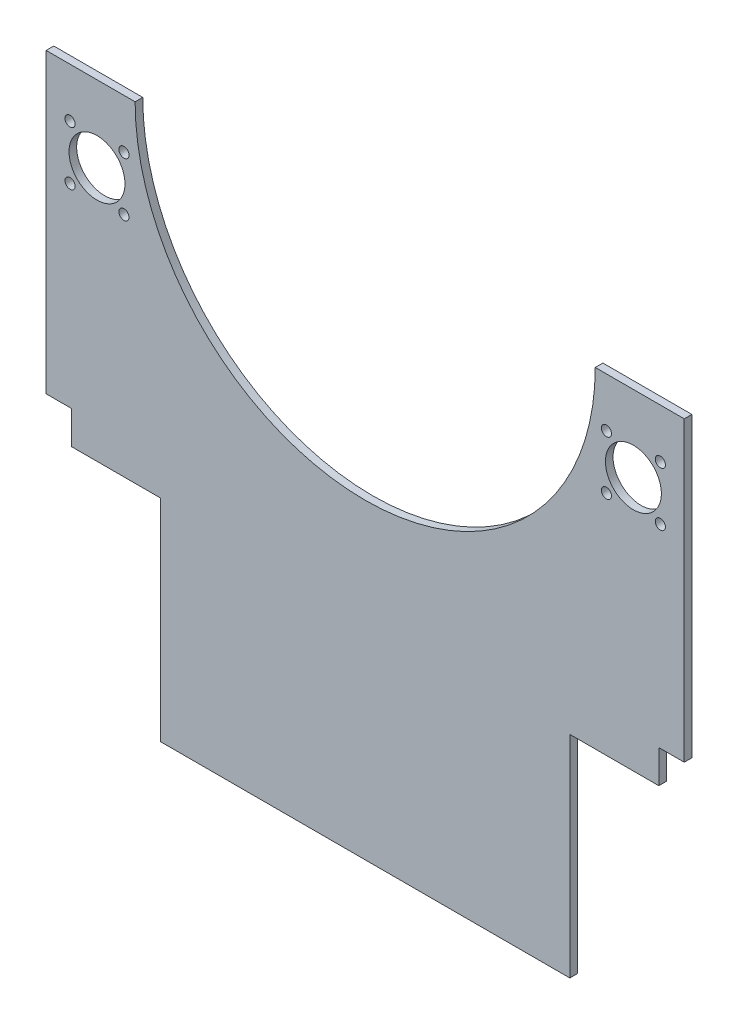
SolidWorks part; units mm, degrees
ref_plane "Plan de face" through (0, 0, 0) normal (0, 0, 1) x (1, 0, 0)
ref_plane "Plan de dessus" through (0, 0, 0) normal (0, 1, 0) x (1, 0, 0)
ref_plane "Plan de droite" through (0, 0, 0) normal (1, 0, 0) x (0, 0, -1)
sketch "Esquisse1" plane through (0, 0, 0) normal (0, 0, 1) x (1, 0, 0)
  line L0 (125.5, 0) -> (125.5, -117)
  line L1 (-90.5, 0) -> (-125.5, 0)
  line L2 (90.5, 0) -> (125.5, 0)
  line L3 (0, 0) -> (0, -135.6456) construction
  line L4 (125.5, -117) -> (115.5, -117)
  line L5 (-80.5, -213) -> (80.5, -213)
  line L6 (-115.5, -130) -> (-80.5, -130)
  line L7 (-80.5, -130) -> (-80.5, -213)
  line L8 (110.5, -30) -> (133.6301, -30) construction
  line L9 (-125.5, -117) -> (-115.5, -117)
  line L10 (80.5, -130) -> (80.5, -213)
  line L11 (-105.5, -30) -> (-105.5, -12.7895) construction
  line L12 (115.5, -117) -> (115.5, -130)
  line L13 (-80.5, -130) -> (80.5, -130) construction
  line L14 (-115.5, -117) -> (-115.5, -130)
  line L15 (115.5, -130) -> (80.5, -130)
  line L16 (-110.5, -30) -> (-133.6301, -30) construction
  line L17 (-125.5, 0) -> (-125.5, -117)
  line L18 (105.5, -30) -> (105.5, -12.7895) construction
  arc A0 (-90.5, 0) -> (90.5, 0) centre (0, 0) ccw
  circle A1 centre (-105.5, -30) radius 11
  circle A2 centre (116.1066, -19.3934) radius 2
  circle A3 centre (94.8934, -40.6066) radius 2
  circle A4 centre (-94.8934, -19.3934) radius 2
  circle A5 centre (-116.1066, -40.6066) radius 2
  circle A6 centre (-94.8934, -40.6066) radius 2
  circle A7 centre (116.1066, -40.6066) radius 2
  circle A8 centre (94.8934, -19.3934) radius 2
  circle A9 centre (105.5, -30) radius 11
  circle A12 centre (-116.1066, -19.3934) radius 2
  dimension "D2" = 83
extrude "Extrusion1" add sketch "Esquisse1" along normal blind 3
